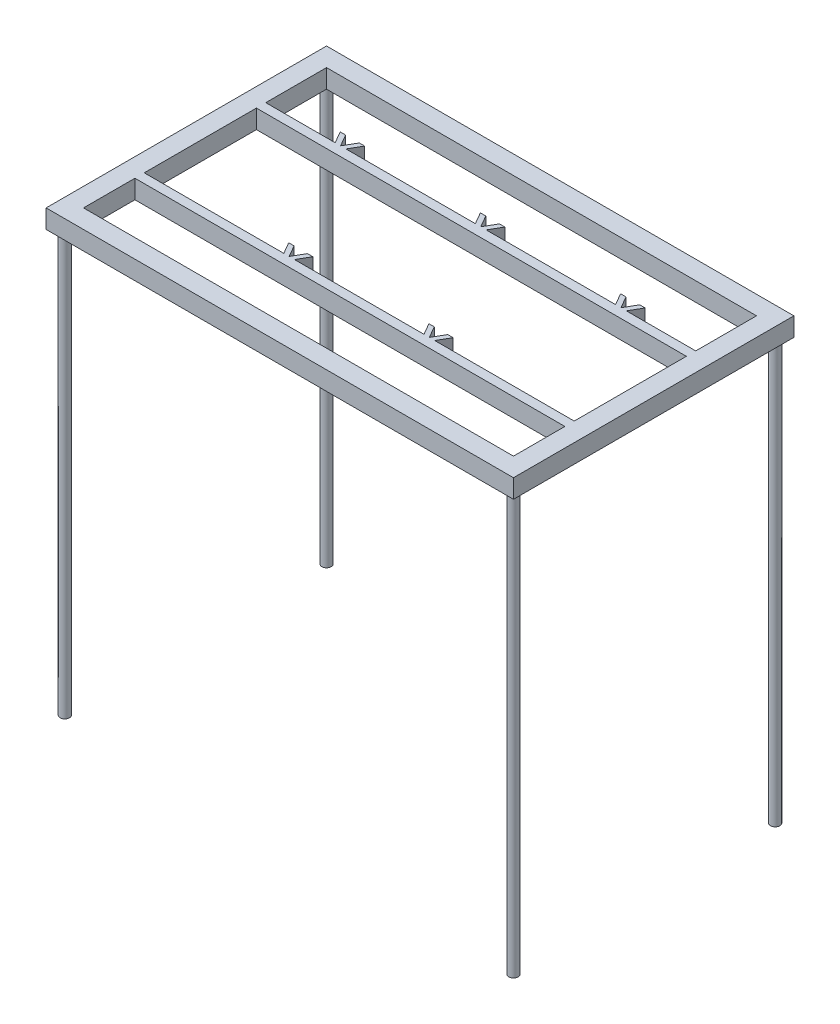
SolidWorks part; units mm, degrees
ref_plane "Front Plane" through (0, 0, 0) normal (0, 0, 1) x (1, 0, 0)
ref_plane "Top Plane" through (0, 0, 0) normal (0, 1, 0) x (1, 0, 0)
ref_plane "Right Plane" through (0, 0, 0) normal (1, 0, 0) x (0, 0, -1)
sketch "Sketch2" plane through (0, 0, 0) normal (0, 1, 0) x (1, 0, 0)
  line L1 (250, 150) -> (-250, 150)
  line L2 (250, 150) -> (250, -150)
  line L3 (250, -150) -> (-250, -150)
  line L4 (-250, 150) -> (-250, -150)
  line L5 (250, 150) -> (-250, -150) construction
  line L6 (250, -150) -> (-250, 150) construction
  point P0 (0, 0)
extrude "Boss-Extrude1" add sketch "Sketch2" along normal blind 20
sketch "Sketch5" plane through (0, 0, 0) normal (0, 1, 0) x (1, 0, 0)
  circle A0 centre (-240, 140) radius 5
  circle A1 centre (240, 140) radius 5
  circle A2 centre (-240, -140) radius 5
  circle A3 centre (240, -140) radius 5
extrude "Boss-Extrude2" add sketch "Sketch5" against normal blind 450
sketch "Sketch6" plane through (0, 0, 0) normal (0, 1, 0) x (1, 0, 0)
  point P0 (0, 0)
sketch "Sketch7" plane through (0, 0, 0) normal (0, -1, 0) x (-1, 0, 0)
  line L1 (-230, 130) -> (230, 130)
  line L2 (-230, 130) -> (-230, -130)
  line L3 (-230, -130) -> (230, -130)
  line L4 (230, 130) -> (230, -130)
  line L5 (-230, 130) -> (230, -130) construction
  line L6 (-230, -130) -> (230, 130) construction
  point P0 (0, 0)
extrude "Cut-Extrude1" cut sketch "Sketch7" against normal blind 20 contours L3 L4 L1 L2
sketch "Sketch8" plane through (0, 0, 0) normal (0, 1, 0) x (1, 0, 0)
  line L0 (-155, 65) -> (-250, 65)
  line L1 (-250, 150) -> (-250, -150) construction
  line L2 (-250, 65) -> (250, 65)
  line L3 (250, -150) -> (250, 150) construction
  line L4 (250, 65) -> (250, 55)
  line L5 (250, 55) -> (-250, 55)
  line L6 (-250, 55) -> (-250, 65)
  line L7 (-80, -65) -> (-250, -65)
  line L8 (-250, -65) -> (250, -65)
  line L9 (250, -65) -> (250, -75)
  line L10 (250, -75) -> (-250, -75)
  line L11 (-250, -75) -> (-250, -65)
extrude "Boss-Extrude3" add sketch "Sketch8" along normal blind 20 contours L2 L4 L5 L6 | L8 L9 L10 L11
sketch "Sketch9" plane through (0, 0, 0) normal (0, 1, 0) x (1, 0, 0)
  line L0 (-150, 77.7209) -> (-150, 65)
  line L1 (-150, 55) -> (-136.8821, 77.7209)
  line L2 (-136.8821, 77.7209) -> (-163.1179, 77.7209)
  line L3 (-163.1179, 77.7209) -> (-150, 55)
  line L4 (-155, 65) -> (-145, 65) construction
  line L5 (13.1179, 77.7209) -> (-13.1179, 77.7209)
  line L6 (0, 55) -> (13.1179, 77.7209)
  line L7 (-13.1179, 77.7209) -> (0, 55)
  line L8 (163.1179, 77.7209) -> (136.8821, 77.7209)
  line L9 (150, 55) -> (163.1179, 77.7209)
  line L10 (136.8821, 77.7209) -> (150, 55)
  circle A0 centre (-150, 70.1473) radius 7.5736 construction
  dimension "D1" = 3
sketch "Sketch13" plane through (0, 20, 0) normal (0, 1, 0) x (1, 0, 0)
  line L0 (75, -74.9296) -> (87.9294, -52.5352)
  line L1 (-75, -74.9296) -> (-62.0706, -52.5352)
  line L2 (-62.0706, -52.5352) -> (-87.9294, -52.5352)
  line L3 (-87.9294, -52.5352) -> (-75, -74.9296)
  line L4 (87.9294, -52.5352) -> (62.0706, -52.5352)
  line L5 (62.0706, -52.5352) -> (75, -74.9296)
  circle A0 centre (-75, -60) radius 7.4648 construction
  dimension "D1" = 2
extrude "Boss-Extrude8" add sketch "Sketch13" against normal blind 20
extrude "Boss-Extrude9" add sketch "Sketch9" along normal blind 20 contours L10 L9 L8 | L7 L6 L5 | L3 L1 L2
sketch "Sketch14" plane through (0, 0, 0) normal (0, 1, 0) x (1, 0, 0)
  line L0 (-136.8821, 77.7209) -> (-163.1179, 77.7209) construction
  line L1 (-150, 65) -> (-138.9834, 84.0814)
  line L2 (-138.9834, 84.0814) -> (-161.0166, 84.0814)
  line L3 (-161.0166, 84.0814) -> (-150, 65)
  line L4 (13.1179, 77.7209) -> (-13.1179, 77.7209) construction
  line L5 (0, 65) -> (11.0166, 84.0814)
  line L6 (11.0166, 84.0814) -> (-11.0166, 84.0814)
  line L7 (-11.0166, 84.0814) -> (0, 65)
  line L8 (163.1179, 77.7209) -> (136.8821, 77.7209) construction
  line L9 (150, 65) -> (161.0166, 84.0814)
  line L10 (161.0166, 84.0814) -> (138.9834, 84.0814)
  line L11 (138.9834, 84.0814) -> (150, 65)
  line L12 (87.9294, -52.5352) -> (62.0706, -52.5352) construction
  line L13 (75, -65) -> (85.7948, -46.3028)
  line L14 (85.7948, -46.3028) -> (64.2052, -46.3028)
  line L15 (64.2052, -46.3028) -> (75, -65)
  line L16 (-62.0706, -52.5352) -> (-87.9294, -52.5352) construction
  line L17 (-75, -65) -> (-64.2052, -46.3028)
  line L18 (-64.2052, -46.3028) -> (-85.7948, -46.3028)
  line L19 (-85.7948, -46.3028) -> (-75, -65)
  circle A0 centre (-150, 77.7209) radius 6.3605 construction
  circle A1 centre (0, 77.7209) radius 6.3605 construction
  circle A2 centre (150, 77.7209) radius 6.3605 construction
  circle A3 centre (75, -52.5352) radius 6.2324 construction
  circle A4 centre (-75, -52.5352) radius 6.2324 construction
extrude "Cut-Extrude6" cut sketch "Sketch14" along normal blind 20
